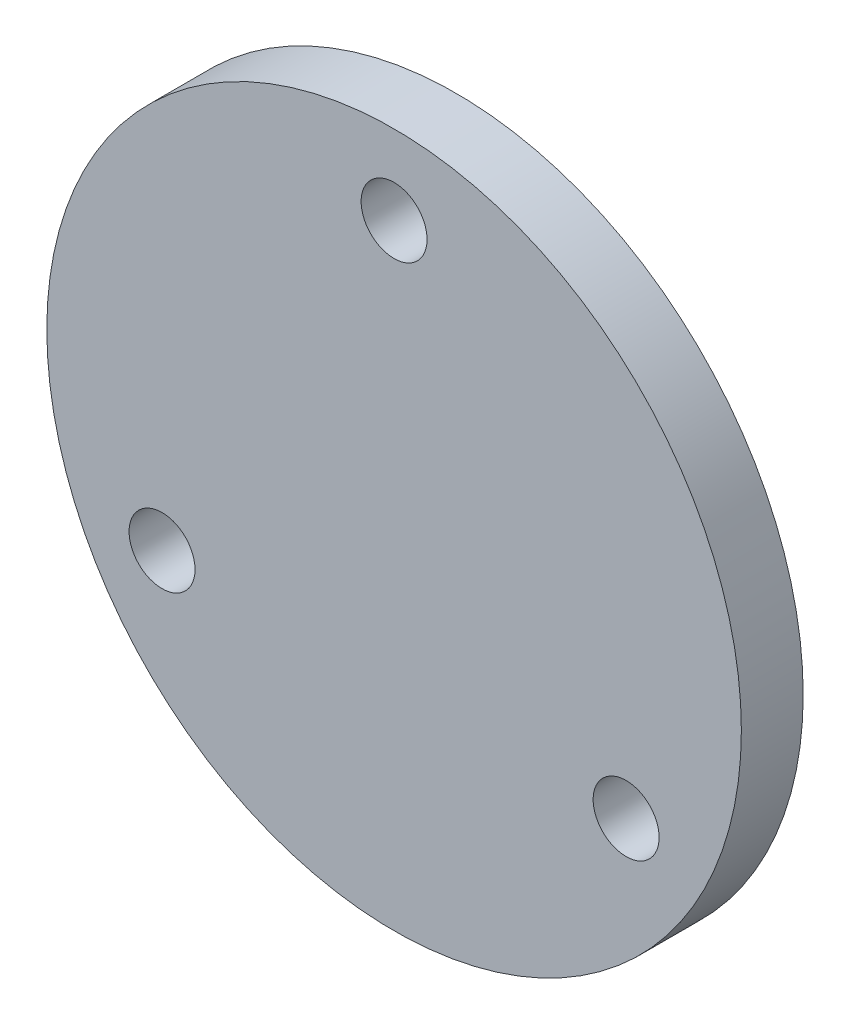
SolidWorks part; units mm, degrees
ref_plane "前视基准面" through (0, 0, 0) normal (0, 0, 1) x (1, 0, 0)
ref_plane "上视基准面" through (0, 0, 0) normal (0, 1, 0) x (1, 0, 0)
ref_plane "右视基准面" through (0, 0, 0) normal (1, 0, 0) x (0, 0, -1)
sketch "草图1" plane through (0, 0, 0) normal (0, 0, 1) x (1, 0, 0)
  line L0 (-10.4002, 0) -> (7.0447, 0) construction
  line L1 (0, 13.1875) -> (0, -10.4324) construction
  line L2 (0, 0) -> (-11.2583, -6.5) construction
  line L3 (0, 0) -> (11.2583, -6.5) construction
  circle A0 centre (0, 0) radius 16.85
  circle A1 centre (0, 13) radius 1.6
  circle A2 centre (11.2583, -6.5) radius 1.6
  circle A3 centre (-11.2583, -6.5) radius 1.6
  point P11 (0, 0)
  dimension "D1" = 33.7
  dimension "D2" = 3.2
  dimension "D3" = 13
  dimension "D5" = 120
  dimension "D4" = 3
extrude "凸台-拉伸1" add sketch "草图1" along normal blind 3
